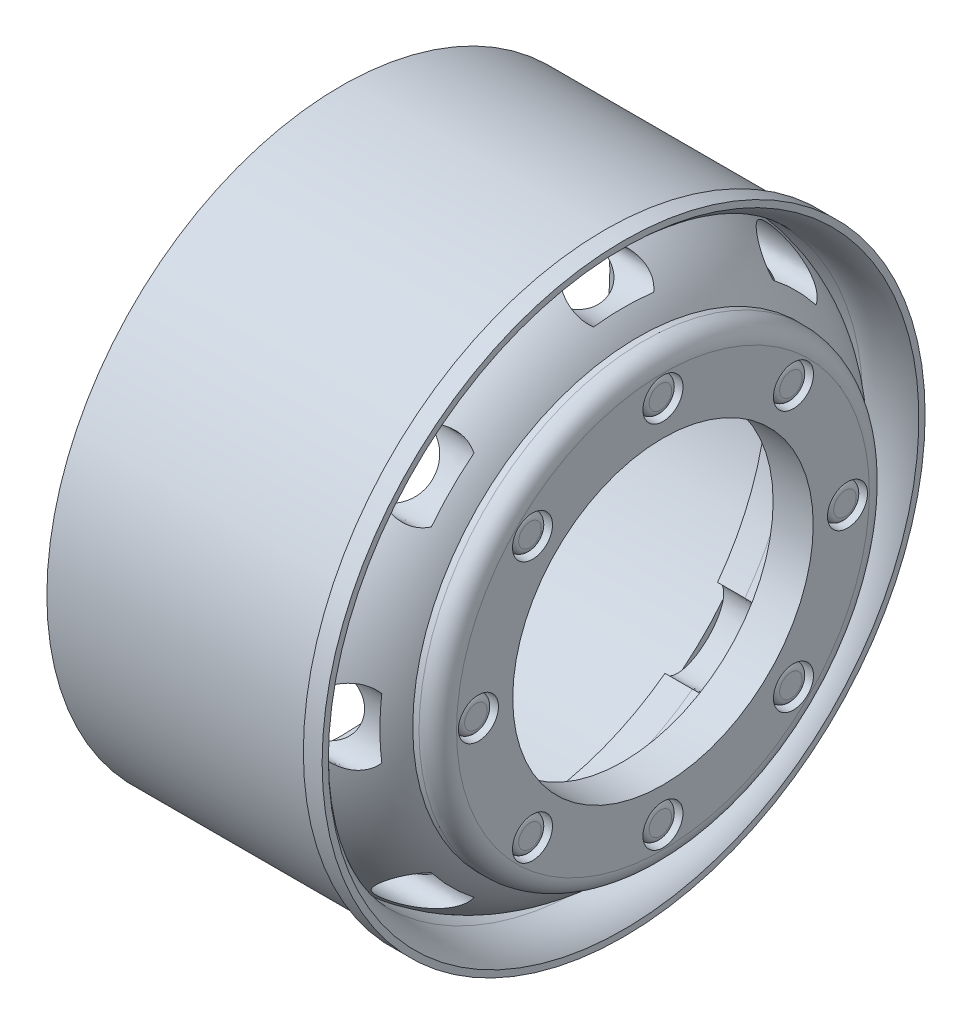
SolidWorks part; units mm, degrees
ref_plane "Front Plane" through (0, 0, 0) normal (0, 0, 1) x (1, 0, 0)
ref_plane "Top Plane" through (0, 0, 0) normal (0, 1, 0) x (1, 0, 0)
ref_plane "Right Plane" through (0, 0, 0) normal (1, 0, 0) x (0, 0, -1)
sketch "Sketch1" plane through (0, 0, 0) normal (0, 0, 1) x (1, 0, 0)
  line L0 (-25, 0) -> (25, 0) construction
  line L1 (0, 36.6286) -> (0, -30.4082) construction
  line L2 (-10, 23.5) -> (11.1, 23.5)
  line L3 (11.1, 23.5) -> (11.1, 24.1)
  line L4 (11.1, 24.1) -> (12.6, 24.1)
  line L5 (12.6, 24.1) -> (12.6, 23.6)
  line L9 (-10, 21.5) -> (-10, 23.5)
  line L27 (9.4257, 22.3) -> (6, 22.3)
  line L36 (13.7458, 18) -> (15.7458, 18)
  line L43 (-10, 21.5) -> (3.8066, 21.5)
  line L44 (6, 20.3) -> (3.8066, 20.3)
  line L45 (3.8066, 20.3) -> (3.8066, 21.5)
  line L47 (12.542, 16) -> (12.542, 8.4837)
  line L48 (-10, 21.5) -> (11.1, 21.5) construction
  line L49 (15.7458, 18) -> (15.7458, 0) construction
  line L51 (13.7458, 16) -> (13.7458, 0) construction
  line L52 (12.542, 8.4837) -> (15.7458, 8.4837)
  line L53 (15.7458, 8.4837) -> (15.7458, 18)
  line L55 (12.542, 16) -> (13.7458, 16) construction
  arc A1 (12.6, 23.6) -> (9.4257, 22.3) centre (9.6236, 26.3422) cw
  arc A4 (6, 22.3) -> (13.7458, 18) centre (6, 13.1735) cw
  arc A5 (6, 20.3) -> (12.542, 16) centre (6, 13.1735) cw
  point P13 (12.9671, 14)
  point P21 (16.5518, 14)
  point P24 (12.9671, 11)
  point P27 (16.5518, 11)
  dimension "D1" = 50
  dimension "D2" = 25
  dimension "D3" = 2
  dimension "D4" = 21.1
  dimension "D5" = 48.2
  dimension "D6" = 0.5
  dimension "D7" = 1.5
  dimension "D9" = 2
  dimension "D10" = 2
  dimension "D11" = 47
revolve "Revolve1" add sketch "Sketch1" angle 360 about L0
sketch "Sketch3" plane through (12.6, 0, 0) normal (1, 0, 0) x (0, 0, -1)
  line L0 (0, 23.6) -> (0, -24.1) construction
  line L1 (-24.1, 0) -> (24.1, 0) construction
  circle A0 centre (0, 0) radius 23.6 construction
  circle A1 centre (0, 0) radius 24.1 construction
  ellipse E0 centre (0, 20.3231) end of major axis (3, 20.3231) minor radius 1.6667
  dimension "D1" = 6
extrude "Cut-Extrude2" cut sketch "Sketch3" against normal up to surface (8.7934 mm away) up to face at (3.8066, 0, 20.3)
pattern_circular "CirPattern1" count 8 over 360 about axis through (15.7458, 0, 0) along (-1, 0, 0) of "Cut-Extrude2"
sketch "Sketch5" plane through (15.7458, 0, 0) normal (1, 0, 0) x (0, 0, -1)
  circle A0 centre (0, 0) radius 14.75 construction
  circle A1 centre (0, 14.75) radius 1.6
  circle A2 centre (10.4298, 10.4298) radius 1.6
  circle A3 centre (14.75, 0) radius 1.6
  circle A4 centre (10.4298, -10.4298) radius 1.6
  circle A5 centre (0, -14.75) radius 1.6
  circle A6 centre (-10.4298, -10.4298) radius 1.6
  circle A7 centre (-14.75, 0) radius 1.6
  circle A8 centre (-10.4298, 10.4298) radius 1.6
  point P22 (0, 0)
  dimension "D1" = 29.5
  dimension "D2" = 3.2
  dimension "D3" = 8
extrude "Cut-Extrude3" cut sketch "Sketch5" against normal offset from surface (1.7038 mm away) 1.5 up to face at (12.542, 0, 8.4837)
sketch "Sketch6" plane through (14.042, 0, 0) normal (1, 0, 0) x (0, 0, -1)
  line L0 (-14.75, 1.6) -> (-14.75, -1.6) construction
  line L1 (-16.35, 0) -> (-13.15, 0) construction
  circle A0 centre (-14.75, 0) radius 1.6 construction
  circle A1 centre (-14.75, 0) radius 1.6 construction
  circle A2 centre (-14.75, 0) radius 1.4
  circle A3 centre (-10.4298, 10.4298) radius 1.4
  circle A4 centre (0, 14.75) radius 1.4
  circle A5 centre (10.4298, 10.4298) radius 1.4
  circle A6 centre (14.75, 0) radius 1.4
  circle A7 centre (10.4298, -10.4298) radius 1.4
  circle A8 centre (0, -14.75) radius 1.4
  circle A9 centre (-10.4298, -10.4298) radius 1.4
  point P28 (0, 0)
  dimension "D1" = 2.8
  dimension "D2" = 8
extrude "Boss-Extrude1" add sketch "Sketch6" along normal blind 1.5
fillet "Fillet1" radius 0.5 8 edges at (15.542, 0, -16.15) (15.542, -10.4298, -11.8298) (15.542, -14.75, -1.4) (15.542, -10.4298, 9.0298) (15.542, 0, 13.35) (15.542, 10.4298, 9.0298) (15.542, 14.75, -1.4) (15.542, 10.4298, -11.8298)
sketch "Sketch7" plane through (15.7458, 0, 0) normal (1, 0, 0) x (0, 0, -1)
  circle A0 centre (0, 0) radius 12.0088
  dimension "D1" = 24.0176
extrude "Cut-Extrude4" cut sketch "Sketch7" against normal through all
fillet "Fillet2" radius 1.5 1 edges at (15.7458, 0, 18)
